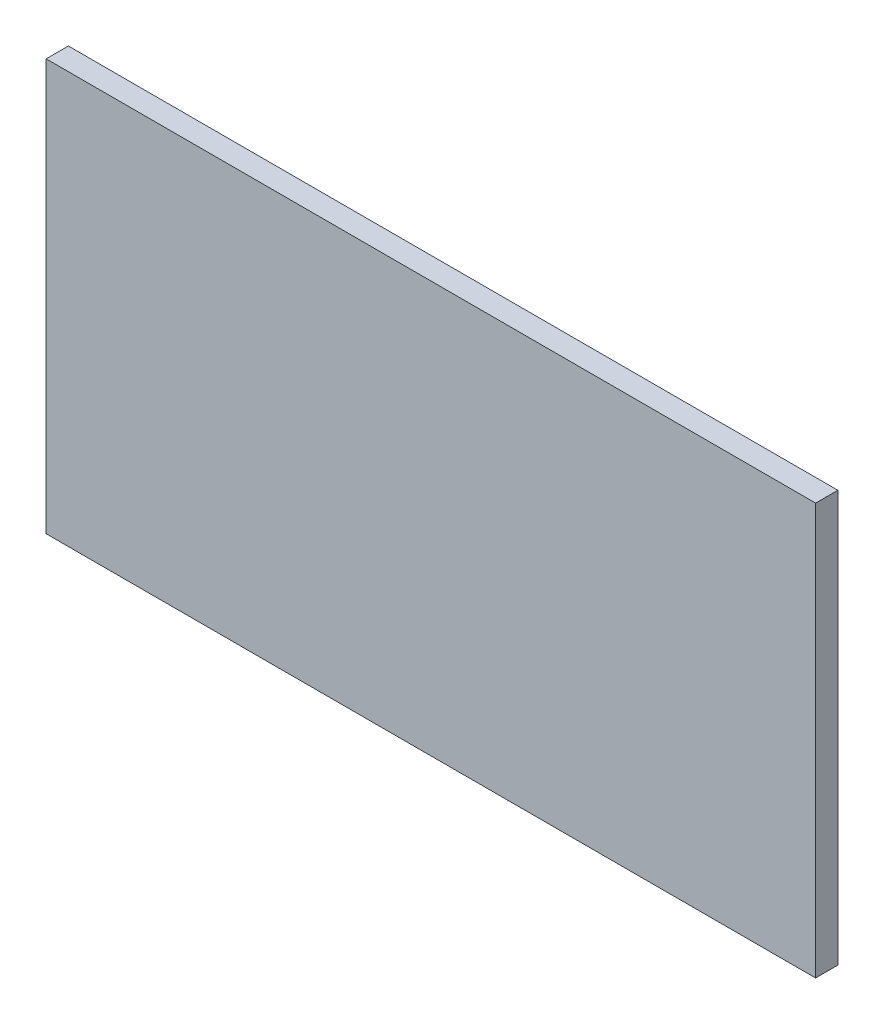
SolidWorks part; units mm, degrees
ref_plane "Front Plane" through (0, 0, 0) normal (0, 0, 1) x (1, 0, 0)
ref_plane "Top Plane" through (0, 0, 0) normal (0, 1, 0) x (1, 0, 0)
ref_plane "Right Plane" through (0, 0, 0) normal (1, 0, 0) x (0, 0, -1)
sketch "Sketch1" plane through (0, 0, 0) normal (0, 0, 1) x (1, 0, 0)
  line L1 (311.5, -166.5) -> (-311.5, -166.5)
  line L2 (311.5, -166.5) -> (311.5, 166.5)
  line L3 (311.5, 166.5) -> (-311.5, 166.5)
  line L4 (-311.5, -166.5) -> (-311.5, 166.5)
  line L5 (311.5, -166.5) -> (-311.5, 166.5) construction
  line L6 (311.5, 166.5) -> (-311.5, -166.5) construction
  point P0 (0, 0)
  dimension "D1" = 333
  dimension "D2" = 623
extrude "Boss-Extrude1" add sketch "Sketch1" along normal blind 18
equation "\"H_DSP\"=18"
equation "\"D1@Boss-Extrude1\"=\"H_DSP\""
